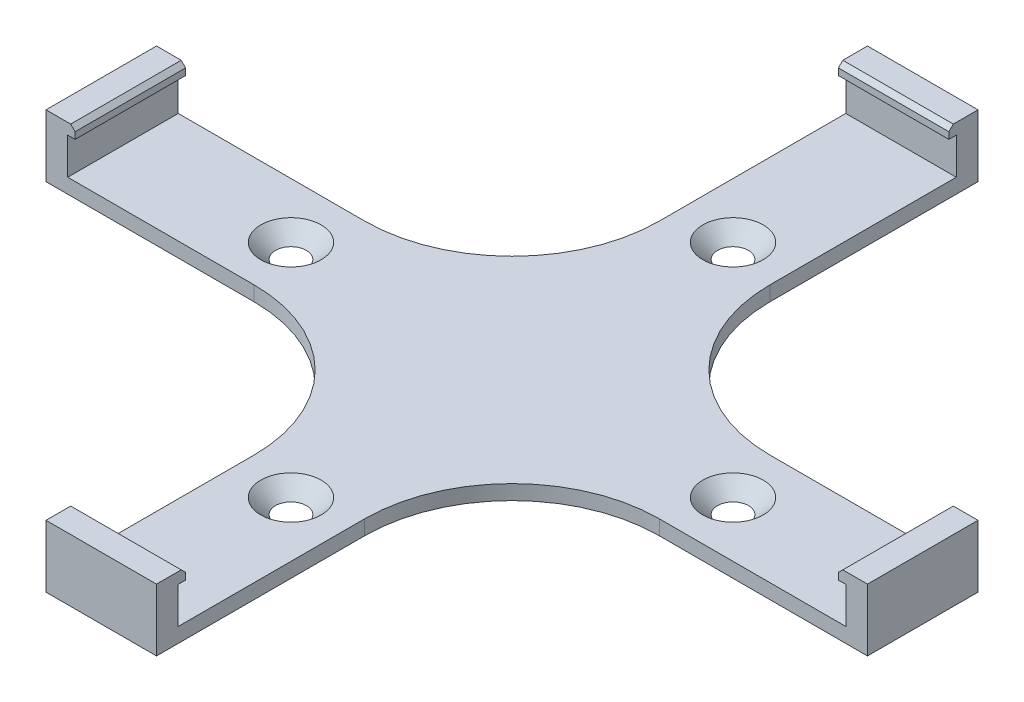
SolidWorks part; units mm, degrees
ref_plane "Front Plane" through (0, 0, 0) normal (0, 0, 1) x (1, 0, 0)
ref_plane "Top Plane" through (0, 0, 0) normal (0, 1, 0) x (1, 0, 0)
ref_plane "Right Plane" through (0, 0, 0) normal (1, 0, 0) x (0, 0, -1)
sketch "Sketch1" plane through (0, 0, 0) normal (0, 1, 0) x (1, 0, 0)
  line L0 (0, 52.8) -> (0, -52.8) construction
  line L1 (-55.75, -55.75) -> (55.75, -55.75) construction
  line L2 (-55.75, -55.75) -> (-55.75, 55.75) construction
  line L3 (-55.75, 55.75) -> (55.75, 55.75) construction
  line L4 (55.75, -55.75) -> (55.75, 55.75) construction
  line L5 (-55.75, -55.75) -> (55.75, 55.75) construction
  line L6 (-55.75, 55.75) -> (55.75, -55.75) construction
  line L7 (-52.8, -52.8) -> (52.8, -52.8) construction
  line L8 (-52.8, -52.8) -> (-52.8, 52.8) construction
  line L9 (-52.8, 52.8) -> (52.8, 52.8) construction
  line L10 (52.8, -52.8) -> (52.8, 52.8) construction
  line L11 (-52.8, -52.8) -> (52.8, 52.8) construction
  line L12 (-52.8, 52.8) -> (52.8, -52.8) construction
  line L13 (-52.8, 0) -> (52.8, 0) construction
  line L14 (-7.5, 55.75) -> (-7.5, 27.5)
  line L15 (-55.75, -7.5) -> (-27.5, -7.5)
  line L16 (7.5, 55.75) -> (7.5, 27.5)
  line L17 (-55.75, 7.5) -> (-27.5, 7.5)
  line L18 (-7.5, 52.8) -> (-7.5, -52.8) construction
  line L19 (7.5, 52.8) -> (7.5, -52.8) construction
  line L20 (-52.8, 7.5) -> (52.8, 7.5) construction
  line L21 (-52.8, -7.5) -> (52.8, -7.5) construction
  line L22 (-7.5, 55.75) -> (7.5, 55.75)
  line L23 (55.75, 7.5) -> (55.75, -7.5)
  line L24 (7.5, -55.75) -> (-7.5, -55.75)
  line L25 (-55.75, -7.5) -> (-55.75, 7.5)
  line L26 (-7.5, -27.5) -> (-7.5, -55.75)
  line L27 (27.5, 7.5) -> (55.75, 7.5)
  line L28 (7.5, -27.5) -> (7.5, -55.75)
  line L29 (27.5, -7.5) -> (55.75, -7.5)
  arc A0 (-27.5, -7.5) -> (-7.5, -27.5) centre (-27.5, -27.5) cw
  arc A1 (7.5, -27.5) -> (27.5, -7.5) centre (27.5, -27.5) cw
  arc A2 (27.5, 7.5) -> (7.5, 27.5) centre (27.5, 27.5) cw
  arc A3 (-7.5, 27.5) -> (-27.5, 7.5) centre (-27.5, 27.5) cw
  point P0 (0, 0)
  point P6 (0, 0)
  point P38 (-7.5, -7.5)
  point P41 (7.5, -7.5)
  point P44 (7.5, 7.5)
  point P47 (-7.5, 7.5)
  dimension "D3" = 20
  dimension "D1" = 111.5
  dimension "D2" = 105.6
extrude "Boss-Extrude1" add sketch "Sketch1" along normal blind 2
sketch "Sketch3" plane through (7.5, 0, 0) normal (1, 0, 0) x (0, 0, -1)
  line L0 (55.75, 2) -> (55.75, 8.45)
  line L1 (55.75, 8.45) -> (52.4, 8.45)
  line L2 (51.8, 7.85) -> (51.8, 6.95)
  line L3 (51.8, 6.95) -> (52.8, 6.95)
  line L4 (52.8, 6.95) -> (52.8, 2)
  line L5 (27.5, 2) -> (55.75, 2) construction
  line L6 (52.8, 2) -> (55.75, 2)
  line L7 (52.4, 8.45) -> (51.8, 7.85)
  point P4 (51.8, 8.45)
  dimension "D1" = 6.45
  dimension "D2" = 1.5
  dimension "D3" = 1
extrude "Boss-Extrude3" add sketch "Sketch3" against normal up to surface (15 mm away) up to face at (-7.5, 1, -41.625)
mirror "Mirror1" about plane through (0, 0, 0) normal (0, 0, 1) of "Boss-Extrude3"
sketch "Sketch6" plane through (0, 0, -7.5) normal (0, 0, -1) x (-1, 0, 0)
  line L0 (55.75, 2) -> (55.75, 8.45)
  line L1 (55.75, 8.45) -> (52.4, 8.45)
  line L2 (51.8, 7.85) -> (51.8, 6.95)
  line L3 (51.8, 6.95) -> (52.8, 6.95)
  line L4 (52.8, 6.95) -> (52.8, 2)
  line L5 (52.8, 2) -> (55.75, 2)
  line L6 (52.4, 8.45) -> (51.8, 7.85)
  point P3 (51.8, 8.45)
  dimension "D1" = 6.45
  dimension "D2" = 1
  dimension "D3" = 1.5
extrude "Boss-Extrude4" add sketch "Sketch6" against normal up to surface (15 mm away) up to face at (-41.625, 1, 7.5)
mirror "Mirror2" about plane through (0, 0, 0) normal (1, 0, 0) of "Boss-Extrude4"
sketch "Sketch7" plane through (0, 2, 0) normal (0, 1, 0) x (1, 0, 0)
  circle A0 centre (0, 0) radius 30
  point P3 (-30, 0)
  point P7 (0, 30)
  point P8 (30, 0)
  point P9 (0, -30)
  point P10 (0, 0)
  dimension "D1" = 60
  dimension "D2" = 4
hole_wizard "CSK for M3.5 Flat Head Machine Screw1" positions "Sketch8" profile "Sketch9" countersink size "M3.5" standard "ANSI Metric" end condition up to next
sketch "Sketch8" plane through (0, 2, 0) normal (0, 1, 0) x (1, 0, 0)
  point P0 (0, -30)
  point P3 (-30, 0)
  point P6 (0, 30)
  point P9 (30, 0)
sketch "Sketch9" plane through (0, 2, 30) normal (1, 0, 0) x (0, 0, 1)
  line L0 (0, 0) -> (0, 2)
  line L1 (0, 2) -> (1.95, 2)
  line L2 (1.95, 2) -> (1.95, 2.15)
  line L3 (1.95, 2.15) -> (4.1, 0)
  line L5 (4.1, 0) -> (0, 0)
  line L6 (-1.95, 2.15) -> (-4.1, 0) construction
  line L11 (0, -6.35) -> (0, 107.95) construction
  dimension "Thru Hole Dia." = 3.9
  dimension "Thru Hole Depth" = 2
  dimension "Near C'Sink Dia." = 8.2
  dimension "Near C'Sink Angle" = 90
sketch "Sketch10" plane through (0, 2, 0) normal (0, 1, 0) x (1, 0, 0)
  line L0 (2.6411, 20.3436) -> (2.6411, -20.3436) construction
  text T0 "BILTEMA\r\n46-2021" font "3ds" height 6
  point P3 (2.6411, 0)
